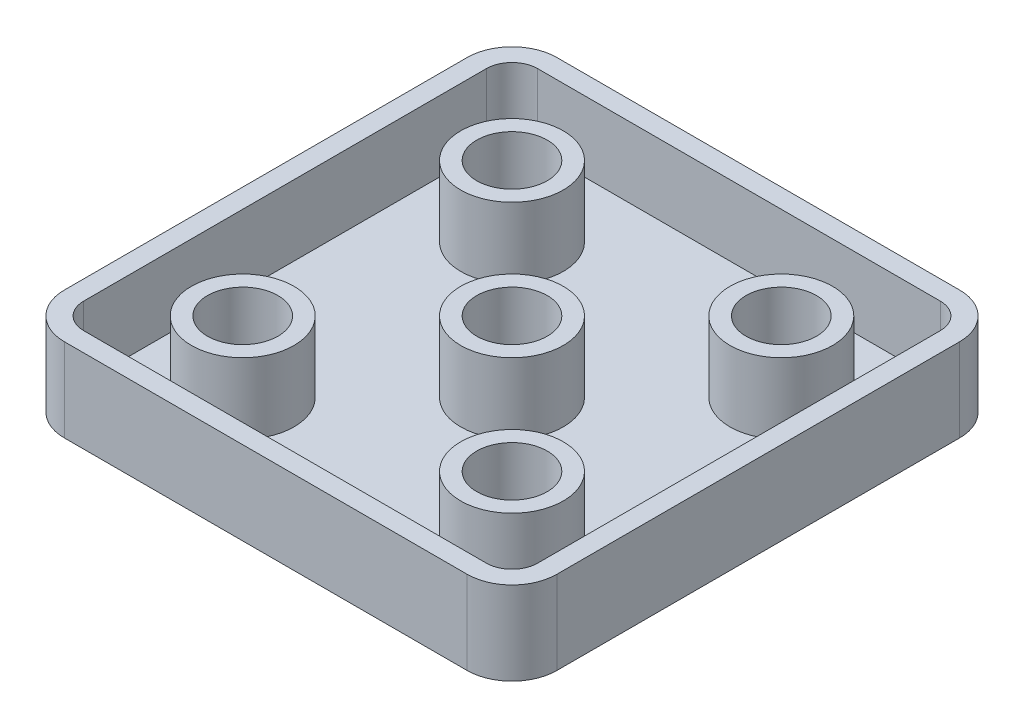
SolidWorks part; units mm, degrees
ref_plane "Front Plane" through (0, 0, 0) normal (0, 0, 1) x (1, 0, 0)
ref_plane "Top Plane" through (0, 0, 0) normal (0, 1, 0) x (1, 0, 0)
ref_plane "Right Plane" through (0, 0, 0) normal (1, 0, 0) x (0, 0, -1)
sketch "Sketch1" plane through (0, 0, 0) normal (0, 1, 0) x (1, 0, 0)
  line L1 (0, 0) -> (-38.4, 0)
  line L2 (0, 0) -> (0, -38.4)
  line L3 (0, -38.4) -> (-38.4, -38.4)
  line L4 (-38.4, 0) -> (-38.4, -38.4)
  dimension "D1" = 38.4
  dimension "D2" = 38.4
  dimension "D3" = 38.4
extrude "Boss-Extrude1" add sketch "Sketch1" along normal blind 6.5
fillet "Fillet1" radius 3.5 4 edges at (-38.4, 3.25, 38.4) (-38.4, 3.25, 0) (0, 3.25, 0) (0, 3.25, 38.4)
sketch "Sketch7" plane through (0, 6.5, 0) normal (0, 1, 0) x (1, 0, 0)
  line L0 (-38.4, -3.5) -> (-38.4, -34.9) construction
  line L1 (-3.5, -36.9) -> (-34.9, -36.9)
  line L2 (-1.5, -34.9) -> (-1.5, -3.5)
  line L3 (-3.5, -1.5) -> (-34.9, -1.5)
  line L4 (-36.9, -34.9) -> (-36.9, -3.5)
  line L5 (-1.5, -36.9) -> (-36.9, -1.5) construction
  line L6 (-1.5, -1.5) -> (-36.9, -36.9) construction
  line L7 (-3.5, 0) -> (-34.9, 0) construction
  line L8 (0, -34.9) -> (0, -3.5) construction
  arc A0 (-34.9, -36.9) -> (-36.9, -34.9) centre (-34.9, -34.9) cw
  arc A1 (-3.5, -36.9) -> (-1.5, -34.9) centre (-3.5, -34.9) ccw
  arc A2 (-1.5, -3.5) -> (-3.5, -1.5) centre (-3.5, -3.5) ccw
  arc A3 (-34.9, -1.5) -> (-36.9, -3.5) centre (-34.9, -3.5) ccw
  circle A4 centre (-29.7, -8.7) radius 4
  circle A5 centre (-29.7, -8.7) radius 2.75
  circle A6 centre (-8.7, -8.7) radius 4
  circle A7 centre (-8.7, -8.7) radius 2.75
  circle A8 centre (-8.7, -29.7) radius 4
  circle A9 centre (-8.7, -29.7) radius 2.75
  circle A10 centre (-29.7, -29.7) radius 4
  circle A11 centre (-29.7, -29.7) radius 2.75
  circle A12 centre (-19.2, -19.2) radius 4
  circle A13 centre (-19.2, -19.2) radius 2.75
  point P0 (-19.2, -19.2)
  dimension "D5" = 2
  dimension "D6" = 8
  dimension "D7" = 5.5
  dimension "D8" = 21
  dimension "D1" = 19.2
  dimension "D2" = 19.2
  dimension "D3" = 1.5
  dimension "D4" = 1.5
  dimension "D9" = 21
extrude "Cut-Extrude1" cut sketch "Sketch7" against normal blind 5.5 contours L3 A3 L4 A0 L1 A1 L2 A2 A12 A10 A8 A6 A4 | A5 | A7 | A13 | A11 | A9
sketch "Sketch8" plane through (0, 1, 0) normal (0, 1, 0) x (1, 0, 0)
  circle A0 centre (-29.7, -29.7) radius 2.75 construction
  circle A1 centre (-8.7, -29.7) radius 2.75 construction
  circle A2 centre (-8.7, -8.7) radius 2.75 construction
  circle A3 centre (-19.2, -19.2) radius 2.75 construction
  circle A4 centre (-29.7, -8.7) radius 2.75 construction
  circle A5 centre (-29.7, -29.7) radius 2.75
  circle A6 centre (-8.7, -29.7) radius 2.75
  circle A7 centre (-8.7, -8.7) radius 2.75
  circle A8 centre (-19.2, -19.2) radius 2.75
  circle A9 centre (-29.7, -8.7) radius 2.75
extrude "Cut-Extrude2" cut sketch "Sketch8" against normal blind 0.4
